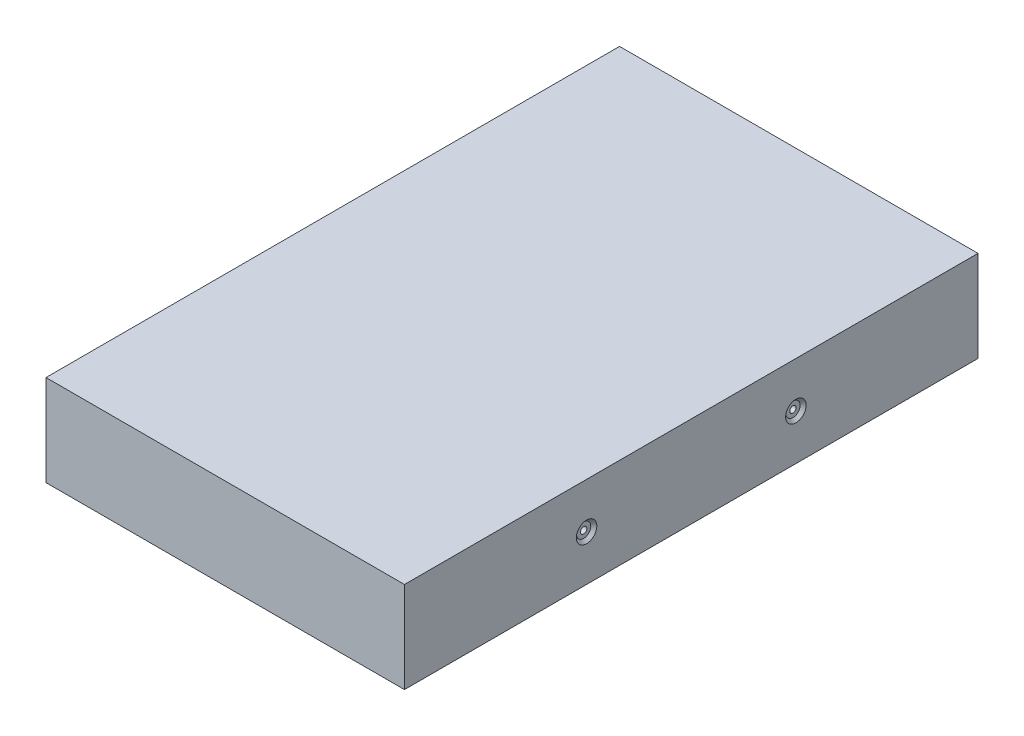
SolidWorks part; units mm, degrees
material "Balsa"
ref_plane "Front Plane" through (0, 0, 0) normal (0, 0, 1) x (1, 0, 0)
ref_plane "Top Plane" through (0, 0, 0) normal (0, 1, 0) x (1, 0, 0)
ref_plane "Right Plane" through (0, 0, 0) normal (1, 0, 0) x (0, 0, -1)
sketch "Sketch1" plane through (0, 0, 0) normal (0, 1, 0) x (1, 0, 0)
  line L1 (-50, 80) -> (50, 80)
  line L2 (-50, 80) -> (-50, -80)
  line L3 (-50, -80) -> (50, -80)
  line L4 (50, 80) -> (50, -80)
  line L5 (-50, 80) -> (50, -80) construction
  line L6 (-50, -80) -> (50, 80) construction
  point P0 (0, 0)
  dimension "D1" = 100
  dimension "D2" = 160
extrude "Boss-Extrude1" add sketch "Sketch1" along normal blind 25.4
hole_wizard "CBORE for #0 Binding Head Machine Screw1" positions "Sketch2" profile "Sketch3" counterbore size "#0" standard "ANSI Inch"
sketch "Sketch2" plane through (50, 0, 0) normal (1, 0, 0) x (0, 0, -1)
  line L0 (-80, 0) -> (80, 0) construction
  line L2 (80, 25.4) -> (80, 0) construction
  point P0 (-29.2, 12.7)
  point P2 (29.2, 12.7)
  dimension "D1" = 12.7
  dimension "D2" = 58.4
  dimension "D3" = 50.8
sketch "Sketch3" plane through (50, 12.7, 29.2) normal (0, 1, 0) x (0, 0, -1)
  line L0 (0, 0) -> (0, 30.5342)
  line L1 (0, 30.5342) -> (0.889, 30)
  line L2 (0.889, 30) -> (0.889, 0.8128)
  line L3 (0.889, 0.8128) -> (1.985, 0.8128)
  line L5 (1.985, 0.8128) -> (1.985, 0.8725)
  line L6 (1.985, 0.8725) -> (2.8575, 0)
  line L7 (2.8575, 0) -> (0, 0)
  line L8 (-1.985, 0.8725) -> (-2.8575, 0) construction
  line L10 (0, 30.5342) -> (-0.889, 30) construction
  line L11 (0, -6.35) -> (0, 107.95) construction
  dimension "Hole Dia." = 1.778
  dimension "Hole Depth" = 30
  dimension "C'Bore Dia." = 3.97
  dimension "C'Bore Depth" = 0.8128
  dimension "Near C'Sink Dia." = 5.715
  dimension "Near C'Sink Angle" = 90
  dimension "Drill Angle" = 118
